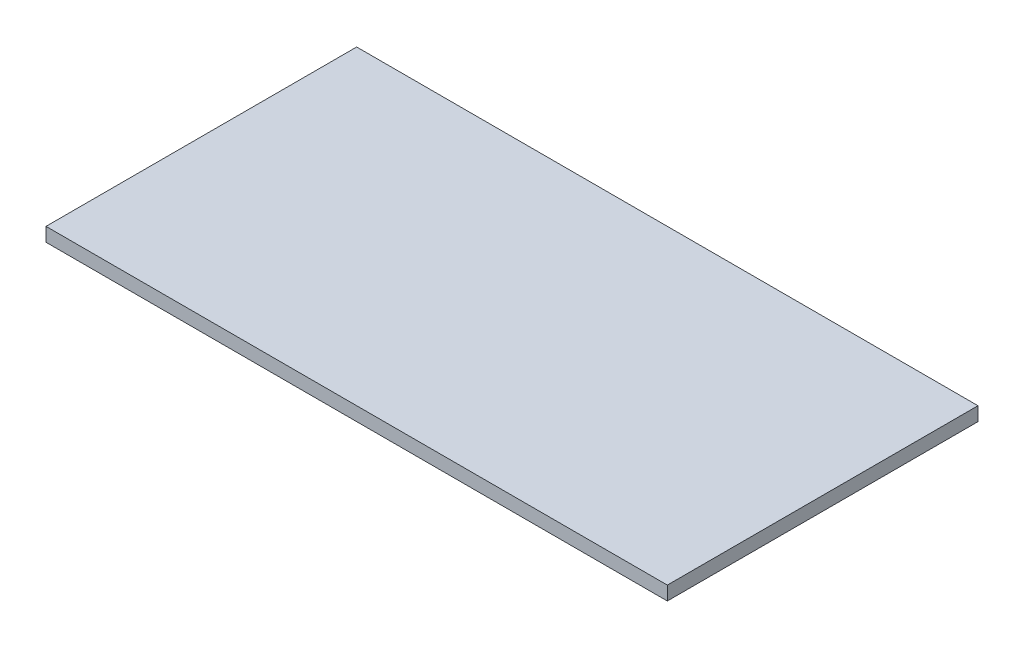
SolidWorks part; units mm, degrees
ref_plane "Front Plane" through (0, 0, 0) normal (0, 0, 1) x (1, 0, 0)
ref_plane "Top Plane" through (0, 0, 0) normal (0, 1, 0) x (1, 0, 0)
ref_plane "Right Plane" through (0, 0, 0) normal (1, 0, 0) x (0, 0, -1)
sketch "Sketch1" plane through (0, 0, 0) normal (0, 1, 0) x (1, 0, 0)
  line L1 (-90, 45) -> (90, 45)
  line L2 (-90, 45) -> (-90, -45)
  line L3 (-90, -45) -> (90, -45)
  line L4 (90, 45) -> (90, -45)
  line L5 (-90, 45) -> (90, -45) construction
  line L6 (-90, -45) -> (90, 45) construction
  point P0 (0, 0)
  dimension "D1" = 90
  dimension "D2" = 180
extrude "Boss-Extrude1" add sketch "Sketch1" along normal blind 4
